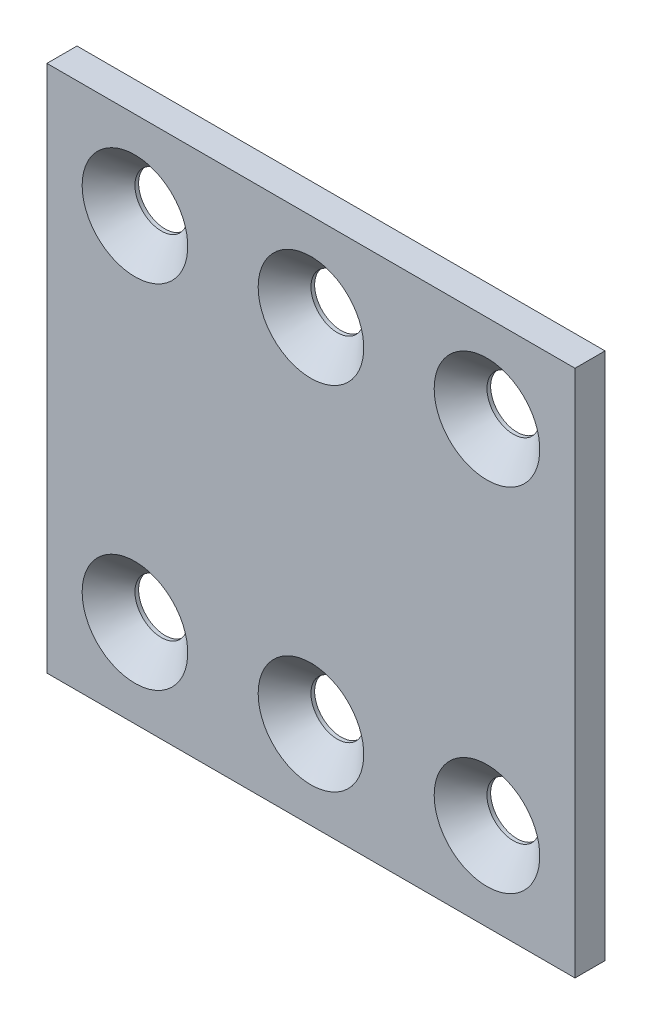
SolidWorks part; units mm, degrees
material "AISI 1010 Steel, hot rolled bar"
ref_plane "Front Plane" through (0, 0, 0) normal (0, 0, 1) x (1, 0, 0)
ref_plane "Top Plane" through (0, 0, 0) normal (0, 1, 0) x (1, 0, 0)
ref_plane "Right Plane" through (0, 0, 0) normal (1, 0, 0) x (0, 0, -1)
sketch "Sketch1" plane through (0, 0, 0) normal (0, 0, 1) x (1, 0, 0)
  line L1 (-30, -30) -> (30, -30)
  line L2 (-30, -30) -> (-30, 30)
  line L3 (-30, 30) -> (30, 30)
  line L4 (30, -30) -> (30, 30)
  line L5 (-30, -30) -> (30, 30) construction
  line L6 (-30, 30) -> (30, -30) construction
  point P1 (0, 0)
  dimension "D2" = 60
  dimension "D3" = 60
extrude "Boss-Extrude1" add sketch "Sketch1" along normal mid plane 3.416
sketch "Sketch2" plane through (0, 0, 1.708) normal (0, 0, 1) x (1, 0, 0)
  line L0 (-20, -20) -> (0, -20) construction
  line L1 (0, -20) -> (20, -20) construction
  line L2 (20, -20) -> (20, 20) construction
  line L3 (20, 20) -> (0, 20) construction
  line L4 (0, 20) -> (-20, 20) construction
  line L5 (-20, 20) -> (-20, -20) construction
  line L6 (-20, -20) -> (20, 20) construction
  line L7 (0, 20) -> (0, 0) construction
  line L8 (0, 0) -> (0, -20) construction
  circle A0 centre (0, 20) radius 3
  circle A1 centre (0, -20) radius 3
  circle A2 centre (20, -20) radius 3
  circle A3 centre (-20, -20) radius 3
  circle A4 centre (-20, 20) radius 3
  circle A5 centre (20, 20) radius 3
  point P13 (0, 0)
  dimension "D1" = 6
  dimension "D2" = 40
  dimension "D3" = 40
extrude "Cut-Extrude1" cut sketch "Sketch2" against normal through all
chamfer "Chamfer1" distance 3 angle 45 6 edges at (23, -20, 1.708) (3, -20, 1.708) (-17, -20, 1.708) (23, 20, 1.708) (3, 20, 1.708) (-17, 20, 1.708)
fillet "Fillet1" [suppressed] radius 1
